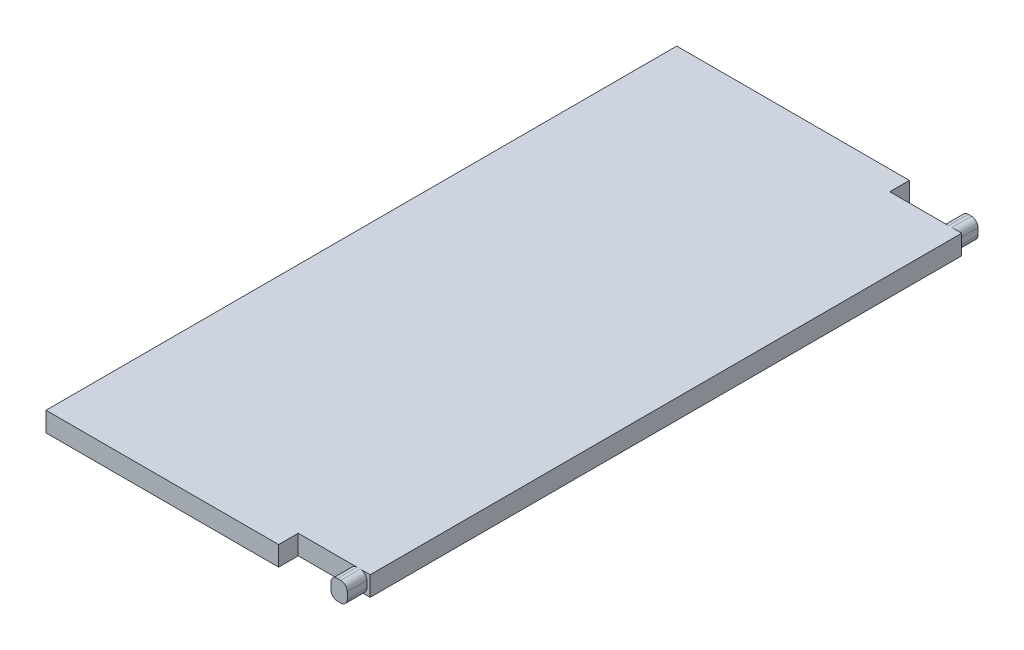
SolidWorks part; units mm, degrees
ref_plane "Front Plane" through (0, 0, 0) normal (0, 0, 1) x (1, 0, 0)
ref_plane "Top Plane" through (0, 0, 0) normal (0, 1, 0) x (1, 0, 0)
ref_plane "Right Plane" through (0, 0, 0) normal (1, 0, 0) x (0, 0, -1)
sketch "Sketch1" plane through (0, 0, 0) normal (0, 1, 0) x (1, 0, 0)
  line L1 (-31.925, 48.26) -> (31.925, 48.26)
  line L2 (-31.925, 48.26) -> (-31.925, -48.26)
  line L3 (-31.925, -48.26) -> (31.925, -48.26)
  line L4 (31.925, 48.26) -> (31.925, -48.26)
  line L5 (-31.925, 48.26) -> (31.925, -48.26) construction
  line L6 (-31.925, -48.26) -> (31.925, 48.26) construction
  point P1 (0, 0)
  dimension "D1" = 63.85
  dimension "D2" = 96.52
extrude "Boss-Extrude1" add sketch "Sketch1" along normal blind 3
sketch "Sketch5" plane through (0, 0, 48.26) normal (0, 0, 1) x (1, 0, 0)
  line L0 (31.925, 3) -> (28.925, 3)
  line L1 (-31.925, 3) -> (31.925, 3) construction
  line L2 (-31.925, 0) -> (31.925, 0) construction
  line L3 (28.925, 3) -> (20.925, 3)
  line L4 (28.925, 3) -> (28.925, 0)
  line L5 (28.925, 0) -> (20.925, 0)
  line L6 (20.925, 3) -> (20.925, 0)
  line M3 (-31.925, 0) -> (31.925, 0)
  line M5 (31.925, 3) -> (-31.925, 3)
  dimension "D1" = 3
  dimension "D2" = 8
extrude "Cut-Extrude3" cut sketch "Sketch5" against normal blind 3 contours L6 L4 M5 M3
sketch "Sketch20" plane through (0, 0, 48.26) normal (0, 0, 1) x (1, 0, 0)
  line L0 (31.425, 3) -> (31.425, 0)
  line L1 (28.925, 3) -> (31.925, 3) construction
  line L2 (28.925, 0) -> (31.925, 0) construction
  line L3 (31.925, 3) -> (31.925, 0) construction
  dimension "D1" = 0.5
extrude "Cut-Extrude6" cut sketch "Sketch20" against normal blind 3 and the other way through all
mirror "Mirror1" about plane through (0, 0, 0) normal (0, 0, 1) of "Cut-Extrude3"
sketch "Sketch21" plane through (0, 0, -48.26) normal (0, 0, -1) x (-1, 0, 0)
  line L0 (-31.425, 3) -> (-31.425, 0)
  line L1 (-31.925, 3) -> (-28.925, 3) construction
  line L2 (-31.925, 0) -> (-28.925, 0) construction
  line L3 (-31.925, 3) -> (-31.925, 0) construction
  line L8 (-31.925, 0) -> (-28.925, 0)
  line L9 (-28.925, 0) -> (-28.925, 3)
  line L10 (-28.925, 3) -> (-31.925, 3)
  line L11 (-31.925, 3) -> (-31.925, 0)
  line L12 (-31.925, 0) -> (-31.425, 0)
  line L14 (-31.425, 3) -> (-31.925, 3)
  line L15 (-31.925, 3) -> (-31.925, 0)
  dimension "D1" = 0.5
  dimension "D2" = 0
extrude "Cut-Extrude11" cut sketch "Sketch21" against normal blind 3
fillet "Fillet17" radius 1 4 edges at (28.925, 0, 46.76) (28.925, 3, 46.76) (31.425, 0, 46.76) (31.425, 3, 46.76)
fillet "Fillet18" radius 1 4 edges at (31.425, 0, -46.76) (31.425, 3, -46.76) (28.925, 0, -46.76) (28.925, 3, -46.76)
sketch "Sketch22" plane through (-31.925, 0, 0) normal (-1, 0, 0) x (0, 0, 1)
  line L1 (-48.26, 3) -> (48.26, 3)
  line L2 (-48.26, 3) -> (-48.26, 0)
  line L3 (-48.26, 0) -> (48.26, 0)
  line L4 (48.26, 3) -> (48.26, 0)
extrude "Cut-Extrude12" cut sketch "Sketch22" against normal blind 17.25
